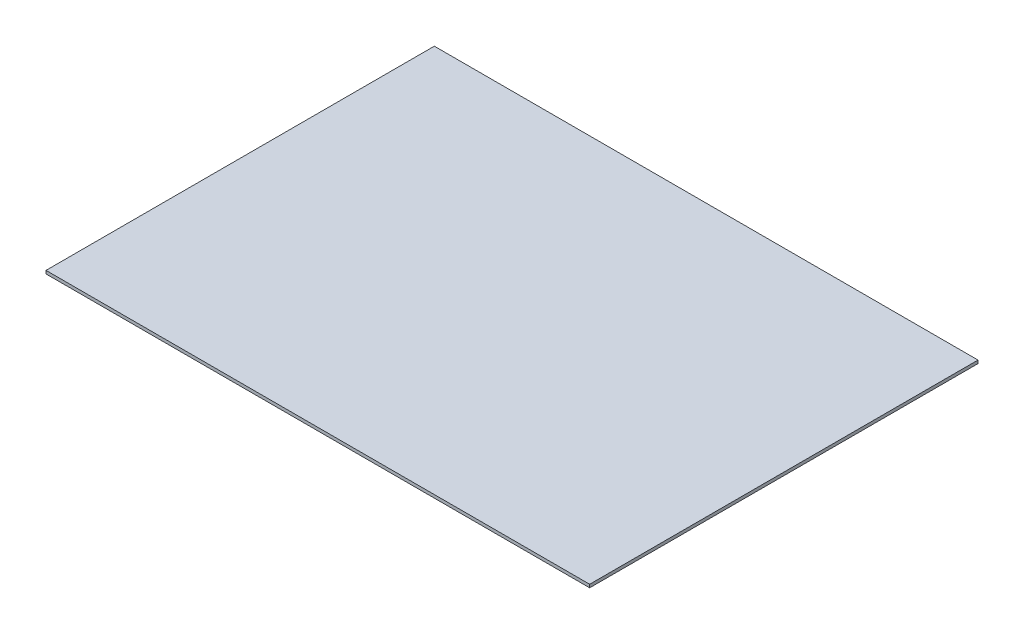
SolidWorks part; units mm, degrees
ref_plane "Front Plane" through (0, 0, 0) normal (0, 0, 1) x (1, 0, 0)
ref_plane "Top Plane" through (0, 0, 0) normal (0, 1, 0) x (1, 0, 0)
ref_plane "Right Plane" through (0, 0, 0) normal (1, 0, 0) x (0, 0, -1)
sketch "Sketch1" plane through (0, 0, 0) normal (0, 1, 0) x (1, 0, 0)
  line L1 (0, 0) -> (350, 0)
  line L2 (0, 0) -> (0, 250)
  line L3 (0, 250) -> (350, 250)
  line L4 (350, 0) -> (350, 250)
extrude "Boss-Extrude1" add sketch "Sketch1" along normal blind 2
